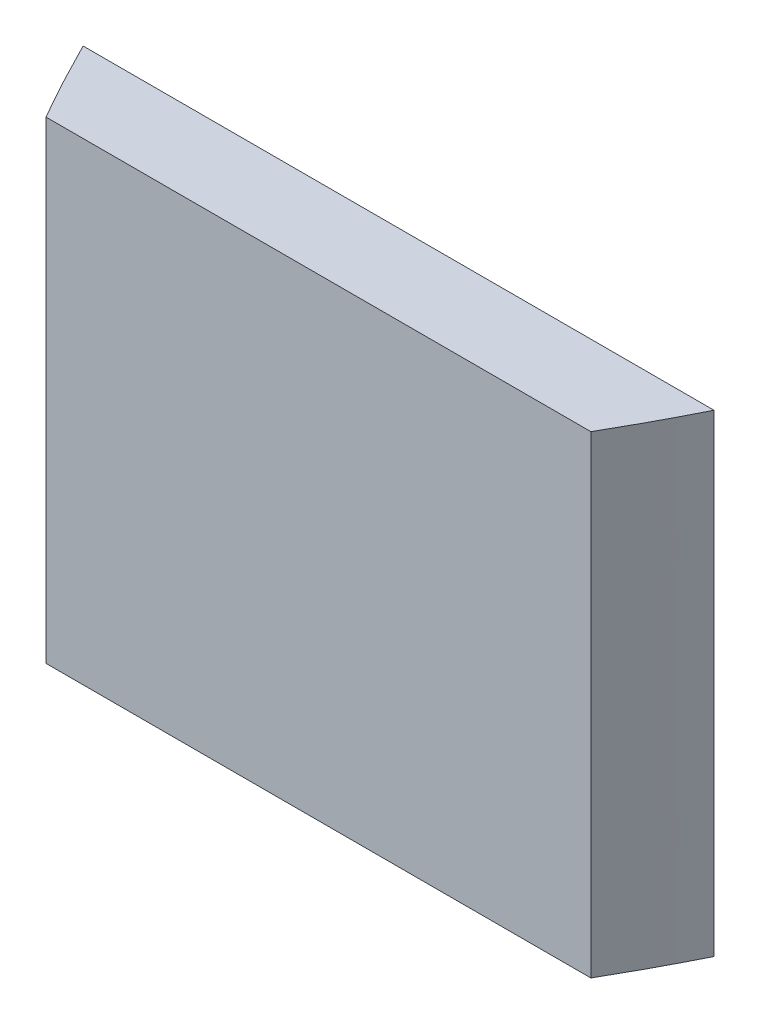
SolidWorks part; units mm, degrees
material "Custom Plastic (2)"
ref_plane "Front Plane" through (0, 0, 0) normal (0, 0, 1) x (1, 0, 0)
ref_plane "Top Plane" through (0, 0, 0) normal (0, 1, 0) x (1, 0, 0)
ref_plane "Right Plane" through (0, 0, 0) normal (1, 0, 0) x (0, 0, -1)
sketch "Sketch1" plane through (0, 0, 0) normal (0, 1, 0) x (1, 0, 0)
  line L0 (-200, 0) -> (200, 0)
  spline S0 degree 2 poles (-225.2396, 53.6645) (0, -453.6645) (225.2396, 53.6645) knots 0 0 0 1 1 1 construction
  spline S1 degree 2 poles (-200, 0) (0, -400) (200, 0) knots 0.056028 0.056028 0.056028 0.943972 0.943972 0.943972
extrude "Boss-Extrude1" add sketch "Sketch1" along normal blind 300
sketch "Sketch7" plane through (0, 300, 0) normal (0, 1, 0) x (1, 0, 0)
  line L0 (200, 0) -> (-200, 0) construction
  line L1 (-219.3305, -50.8) -> (241.9054, -50.8)
  line L2 (-219.3305, -50.8) -> (-219.3305, -250.8)
  line L3 (-219.3305, -250.8) -> (241.9054, -250.8)
  line L4 (241.9054, -50.8) -> (241.9054, -250.8)
  dimension "D1" = 50.8
  dimension "D2" = 200
extrude "Cut-Extrude5" cut sketch "Sketch7" against normal blind 350 contours L3 L4 L1 L2
